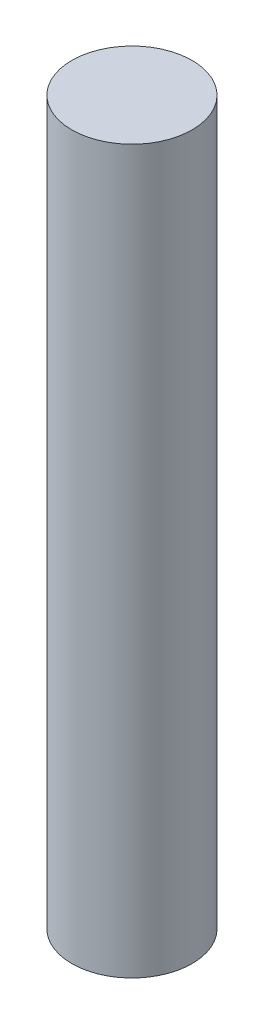
SolidWorks part; units mm, degrees
ref_plane "Front Plane" through (0, 0, 0) normal (0, 0, 1) x (1, 0, 0)
ref_plane "Top Plane" through (0, 0, 0) normal (0, 1, 0) x (1, 0, 0)
ref_plane "Right Plane" through (0, 0, 0) normal (1, 0, 0) x (0, 0, -1)
sketch "Sketch2" plane through (0, 0, 0) normal (0, 1, 0) x (1, 0, 0)
  circle A0 centre (0, 0) radius 2.5
  dimension "D1" = 5
extrude "Boss-Extrude1" add sketch "Sketch2" along normal blind 30
